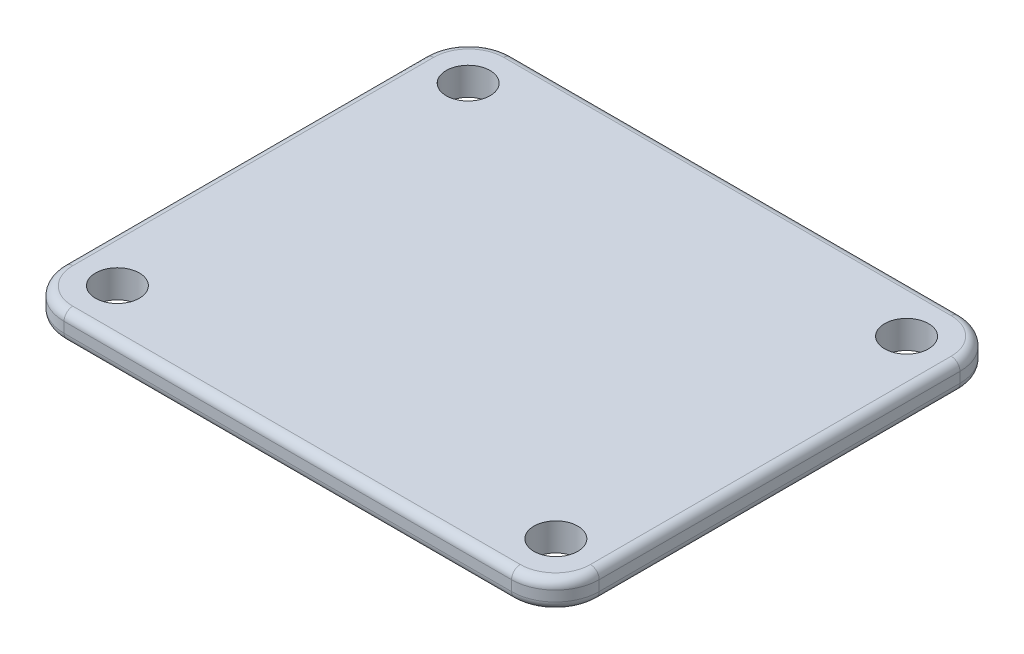
SolidWorks part; units mm, degrees
ref_plane "Front Plane" through (0, 0, 0) normal (0, 0, 1) x (1, 0, 0)
ref_plane "Top Plane" through (0, 0, 0) normal (0, 1, 0) x (1, 0, 0)
ref_plane "Right Plane" through (0, 0, 0) normal (1, 0, 0) x (0, 0, -1)
sketch "Sketch1" plane through (0, 0, 0) normal (0, 1, 0) x (1, 0, 0)
  line L96 (-67.7014, -26.5886) -> (-118.7325, -26.5907)
  line L97 (-123.7327, -21.5907) -> (-123.7327, 19.5533)
  line L98 (-118.7327, 24.5533) -> (-67.7022, 24.5535)
  line L99 (-62.7022, 19.5536) -> (-62.7016, -21.5886)
  circle A0 centre (-118.2172, 18.9813) radius 2.4998
  circle A1 centre (-68.2177, 18.9815) radius 2.4998
  circle A2 centre (-68.2171, -21.0167) radius 2.4998
  circle A3 centre (-118.2172, -21.0186) radius 2.4998
  arc A4 (-123.7327, 19.5533) -> (-118.7327, 24.5533) centre (-118.7327, 19.5533) cw
  arc A5 (-67.7022, 24.5535) -> (-62.7022, 19.5536) centre (-67.7022, 19.5535) cw
  arc A6 (-62.7016, -21.5886) -> (-67.7014, -26.5886) centre (-67.7016, -21.5886) cw
  arc A7 (-118.7325, -26.5907) -> (-123.7327, -21.5907) centre (-118.7327, -21.5907) cw
  point P2 (-123.7327, 24.5533)
  point P6 (-62.7022, 24.5535)
  point P13 (-123.7327, -26.5909)
  dimension "D13" = 5
  dimension "D14" = 5
  dimension "D1" = 61.0304
  dimension "D2" = 51.1442
  dimension "D3" = 5.5155
  dimension "D4" = 5.572
  dimension "D5" = 5.572
  dimension "D6" = 5.5155
  dimension "D7" = 5.5155
  dimension "D8" = 5.572
  dimension "D9" = 5.5155
  dimension "D10" = 5.572
  dimension "D11" = 40
  dimension "D12" = 50.0001
extrude "Boss-Extrude1" add sketch "Sketch1" along normal blind 3.175
fillet "Fillet1" radius 1 16 edges at (-122.2681, 0, 25.1263) (-123.7327, 0, 1.0187) (-122.2682, 0, -23.0889) (-93.2174, 0, -24.5534) (-64.1667, 0, -23.0891) (-62.7019, 0, 1.0175) (-64.1659, 0, 25.1241) (-122.2681, 3.175, 25.1263) (-123.7327, 3.175, 1.0187) (-122.2682, 3.175, -23.0889) (-93.2174, 3.175, -24.5534) (-64.1667, 3.175, -23.0891) (-62.7019, 3.175, 1.0175) (-64.1659, 3.175, 25.1241) (-93.2169, 0, 26.5896) (-93.2169, 3.175, 26.5896)
equation "\"D8@Sketch1\" = \"D5@Sketch1\""
equation "\"D10@Sketch1\" = \"D4@Sketch1\""
equation "\"D3@Sketch1\" = \"D6@Sketch1\""
equation "\"D9@Sketch1\" = \"D6@Sketch1\""
equation "\"D7@Sketch1\" = \"D6@Sketch1\""
